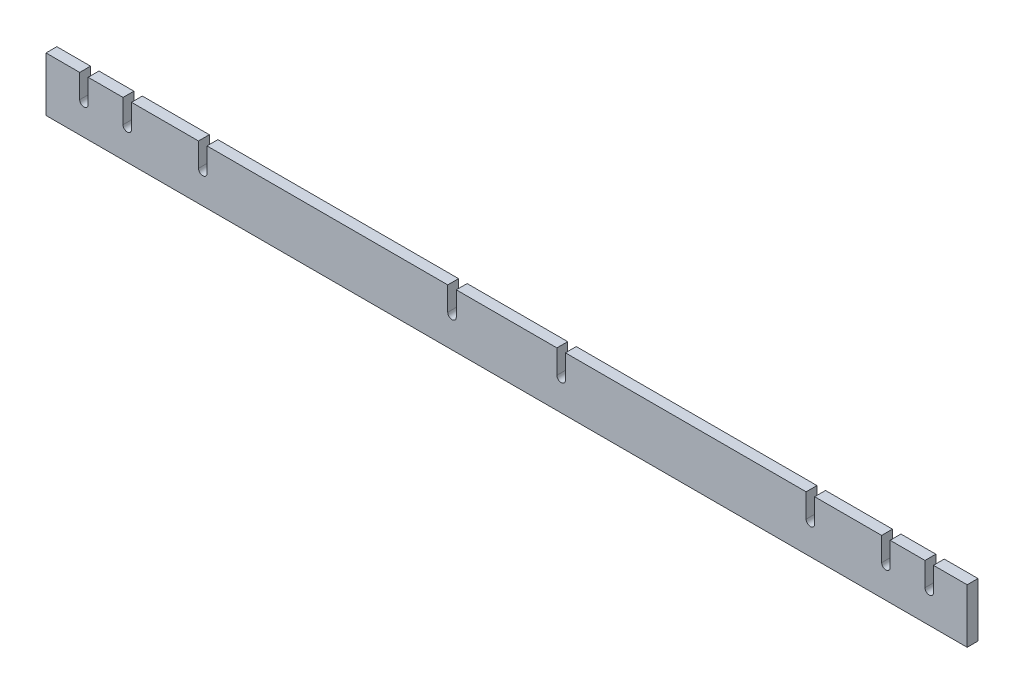
SolidWorks part; units mm, degrees
ref_plane "Front Plane" through (0, 0, 0) normal (0, 0, 1) x (1, 0, 0)
ref_plane "Top Plane" through (0, 0, 0) normal (0, 1, 0) x (1, 0, 0)
ref_plane "Right Plane" through (0, 0, 0) normal (1, 0, 0) x (0, 0, -1)
sketch "Sketch1" plane through (0, 0, 0) normal (0, 0, 1) x (1, 0, 0)
  line L0 (0, 0) -> (0, 1089.0775) construction
  line L3 (-539.75, 1028.7) -> (539.75, 1028.7)
  line L4 (-539.75, 1028.7) -> (-539.75, 965.2)
  line L5 (-539.75, 965.2) -> (539.75, 965.2)
  line L6 (0, 1028.7) -> (0, 965.2) construction
  line L7 (584.2, 0) -> (-584.2, 0) construction
  line L8 (539.75, 1028.7) -> (539.75, 965.2)
  dimension "D1" = 1028.7
  dimension "D2" = 63.5
  dimension "D3" = 1079.5
extrude "Extrude1" add sketch "Sketch1" along normal blind 12.7
sketch "Sketch4" plane through (0, 0, 0) normal (0, 0, -1) x (-1, 0, 0)
  line L0 (-68.95, 1028.7) -> (-68.95, 1000.9)
  line L1 (-351.05, 1028.7) -> (-361.05, 1028.7)
  line L2 (-361.05, 1028.7) -> (-361.05, 1000.9)
  line L3 (-361.05, 995.9) -> (-351.05, 995.9) construction
  line L4 (-351.05, 1028.7) -> (-351.05, 1000.9)
  line L5 (-58.95, 1028.7) -> (-58.95, 1000.9)
  line L6 (58.95, 1028.7) -> (58.95, 1000.9)
  line L7 (68.95, 1028.7) -> (68.95, 1000.9)
  line L8 (351.05, 1028.7) -> (351.05, 1000.9)
  line L9 (361.05, 1028.7) -> (361.05, 1000.9)
  line L10 (361.05, 1028.7) -> (351.05, 1028.7)
  line L12 (68.95, 1028.7) -> (58.95, 1028.7)
  line L13 (-58.95, 1028.7) -> (-68.95, 1028.7)
  line L14 (-539.75, 1028.7) -> (539.75, 1028.7) construction
  circle A0 centre (-356.05, 1000.9) radius 5 construction
  circle A1 centre (-63.95, 1000.9) radius 5 construction
  circle A3 centre (63.95, 1000.9) radius 5 construction
  circle A4 centre (356.05, 1000.9) radius 5 construction
  arc A5 (-361.05, 1000.9) -> (-351.05, 1000.9) centre (-356.05, 1000.9) ccw
  arc A7 (-68.95, 1000.9) -> (-58.95, 1000.9) centre (-63.95, 1000.9) ccw
  arc A9 (58.95, 1000.9) -> (68.95, 1000.9) centre (63.95, 1000.9) ccw
  arc A11 (351.05, 1000.9) -> (361.05, 1000.9) centre (356.05, 1000.9) ccw
  dimension "D1" = 10
extrude "Cut-Extrude1" cut sketch "Sketch4" against normal through all
sketch "Sketch6" plane through (0, 0, 0) normal (0, 0, -1) x (-1, 0, 0)
  line L0 (-449.453, 1028.7) -> (-439.547, 1028.7)
  line L1 (439.547, 1028.7) -> (449.453, 1028.7)
  line L2 (-539.75, 1028.7) -> (-361.05, 1028.7) construction
  line L7 (361.05, 1028.7) -> (539.75, 1028.7) construction
  line L11 (490.347, 1001.014) -> (490.347, 1028.7)
  line L12 (500.253, 1001.014) -> (500.253, 1028.7)
  line L13 (490.347, 1028.7) -> (500.253, 1028.7)
  line L14 (439.547, 1001.014) -> (439.547, 1028.7)
  line L15 (449.453, 1001.014) -> (449.453, 1028.7)
  line L17 (-439.547, 1001.014) -> (-439.547, 1028.7)
  line L19 (-449.453, 1028.7) -> (-449.453, 1001.014)
  line L20 (-490.347, 1001.014) -> (-490.347, 1028.7)
  line L21 (-490.347, 1028.7) -> (-500.253, 1028.7)
  line L22 (-500.253, 1028.7) -> (-500.253, 1001.014)
  arc A0 (-449.453, 1001.014) -> (-439.547, 1001.014) centre (-444.5, 1001.014) ccw
  arc A1 (-500.253, 1001.014) -> (-490.347, 1001.014) centre (-495.3, 1001.014) ccw
  arc A2 (439.547, 1001.014) -> (449.453, 1001.014) centre (444.5, 1001.014) ccw
  arc A3 (490.347, 1001.014) -> (500.253, 1001.014) centre (495.3, 1001.014) ccw
  dimension "D1" = 9.906
  dimension "D5" = 9.906
  dimension "D6" = 9.906
  dimension "D7" = 9.906
  dimension "D3" = 50.8
  dimension "D4" = 27.686
  dimension "D9" = 50.8
extrude "Cut-Extrude2" cut sketch "Sketch6" against normal blind 20.32
